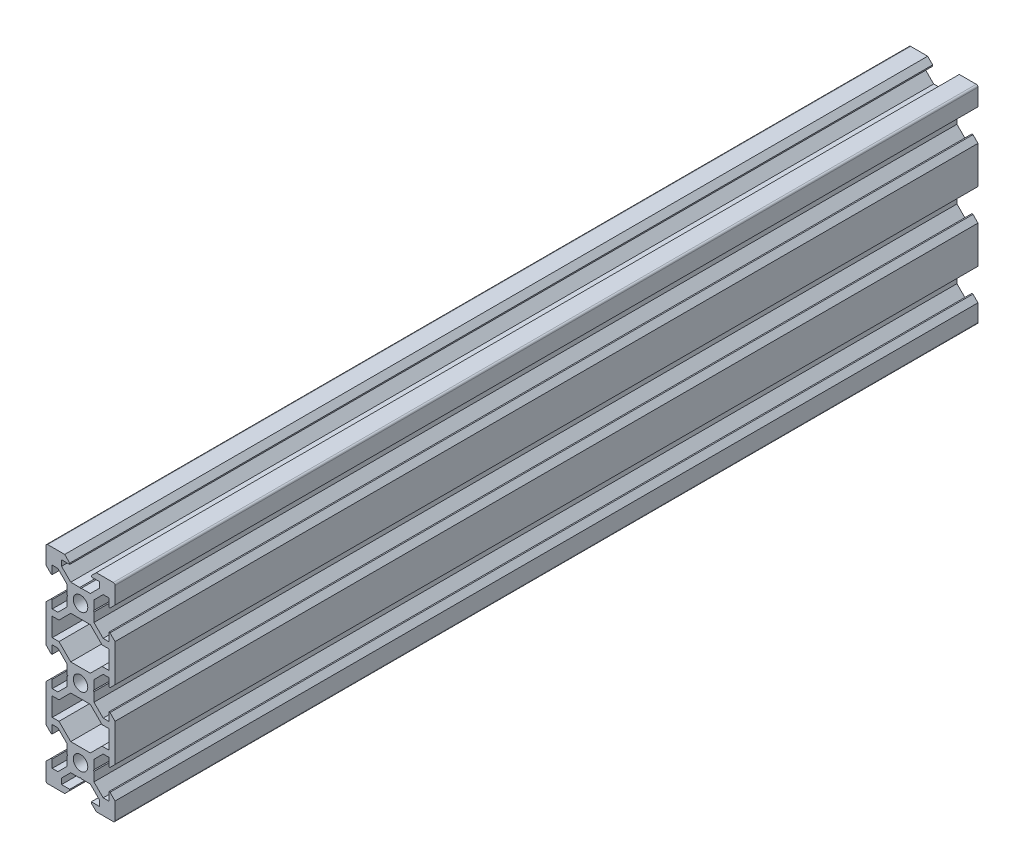
SolidWorks part; units mm, degrees
material "6061-T6 (SS)"
ref_plane "Front Plane" through (0, 0, 0) normal (0, 0, 1) x (1, 0, 0)
ref_plane "Top Plane" through (0, 0, 0) normal (0, 1, 0) x (1, 0, 0)
ref_plane "Right Plane" through (0, 0, 0) normal (1, 0, 0) x (0, 0, -1)
sketch "Sketch1" plane through (0, 0, 0) normal (0, 0, 1) x (1, 0, 0)
  line L0 (0, 0) -> (10, 0) construction
  line L1 (9.5, -30) -> (-9.5, -30)
  line L2 (10, -29.5) -> (10, 29.5)
  line L3 (9.5, 30) -> (-9.5, 30)
  line L4 (-10, -29.5) -> (-10, 29.5)
  line L5 (10, -30) -> (-10, 30) construction
  line L6 (10, 30) -> (-10, -30) construction
  circle A0 centre (0, 20) radius 2.1
  circle A1 centre (0, 0) radius 2.1
  circle A2 centre (0, -20) radius 2.1
  arc A3 (-9.5, -30) -> (-10, -29.5) centre (-9.5, -29.5) cw
  arc A4 (9.5, -30) -> (10, -29.5) centre (9.5, -29.5) ccw
  arc A5 (10, 29.5) -> (9.5, 30) centre (9.5, 29.5) ccw
  arc A6 (-9.5, 30) -> (-10, 29.5) centre (-9.5, 29.5) ccw
  point P0 (0, 0)
  line B0 (0, 20) -> (0, 30) construction
  line B1 (0, 23.69) -> (-0.21, 23.9)
  line B2 (-0.21, 23.9) -> (-2.8393, 23.9)
  line B3 (-2.8393, 23.9) -> (-5.5, 26.5607)
  line B4 (-5.5, 26.5607) -> (-5.5, 28.2)
  line B5 (-5.5, 28.2) -> (-3.125, 28.2)
  line B6 (-3.125, 28.2) -> (-3.125, 28.545)
  line B7 (-3.125, 28.545) -> (-4.58, 30)
  line B8 (-4.58, 30) -> (4.58, 30)
  line B9 (0, 20) -> (-5.9132, 25.9132) construction
  line B10 (3.125, 28.545) -> (4.58, 30)
  line B11 (3.125, 28.2) -> (3.125, 28.545)
  line B12 (5.5, 28.2) -> (3.125, 28.2)
  line B13 (5.5, 26.5607) -> (5.5, 28.2)
  line B14 (2.8393, 23.9) -> (5.5, 26.5607)
  line B15 (0.21, 23.9) -> (2.8393, 23.9)
  line B16 (0, 23.69) -> (0.21, 23.9)
  line B17 (0, 20) -> (-10, 20) construction
  line B18 (-3.69, 20) -> (-3.9, 19.79)
  line B19 (-3.9, 19.79) -> (-3.9, 17.1607)
  line B20 (-3.9, 17.1607) -> (-6.5607, 14.5)
  line B21 (-6.5607, 14.5) -> (-8.2, 14.5)
  line B22 (-8.2, 14.5) -> (-8.2, 16.875)
  line B23 (-8.2, 16.875) -> (-8.545, 16.875)
  line B24 (-8.545, 16.875) -> (-10, 15.42)
  line B25 (-10, 15.42) -> (-10, 24.58)
  line B26 (0, 20) -> (-5.9132, 14.0868) construction
  line B27 (-8.545, 23.125) -> (-10, 24.58)
  line B28 (-8.2, 23.125) -> (-8.545, 23.125)
  line B29 (-8.2, 25.5) -> (-8.2, 23.125)
  line B30 (-6.5607, 25.5) -> (-8.2, 25.5)
  line B31 (-3.9, 22.8393) -> (-6.5607, 25.5)
  line B32 (-3.9, 20.21) -> (-3.9, 22.8393)
  line B33 (-3.69, 20) -> (-3.9, 20.21)
  line B34 (0, 0) -> (-10, 0) construction
  line B35 (-3.69, 0) -> (-3.9, -0.21)
  line B36 (-3.9, -0.21) -> (-3.9, -2.8393)
  line B37 (-3.9, -2.8393) -> (-6.5607, -5.5)
  line B38 (-6.5607, -5.5) -> (-8.2, -5.5)
  line B39 (-8.2, -5.5) -> (-8.2, -3.125)
  line B40 (-8.2, -3.125) -> (-8.545, -3.125)
  line B41 (-8.545, -3.125) -> (-10, -4.58)
  line B42 (-10, -4.58) -> (-10, 4.58)
  line B43 (0, 0) -> (-5.9132, -5.9132) construction
  line B44 (-8.545, 3.125) -> (-10, 4.58)
  line B45 (-8.2, 3.125) -> (-8.545, 3.125)
  line B46 (-8.2, 5.5) -> (-8.2, 3.125)
  line B47 (-6.5607, 5.5) -> (-8.2, 5.5)
  line B48 (-3.9, 2.8393) -> (-6.5607, 5.5)
  line B49 (-3.9, 0.21) -> (-3.9, 2.8393)
  line B50 (-3.69, 0) -> (-3.9, 0.21)
  line B51 (0, -20) -> (-10, -20) construction
  line B52 (-3.69, -20) -> (-3.9, -20.21)
  line B53 (-3.9, -20.21) -> (-3.9, -22.8393)
  line B54 (-3.9, -22.8393) -> (-6.5607, -25.5)
  line B55 (-6.5607, -25.5) -> (-8.2, -25.5)
  line B56 (-8.2, -25.5) -> (-8.2, -23.125)
  line B57 (-8.2, -23.125) -> (-8.545, -23.125)
  line B58 (-8.545, -23.125) -> (-10, -24.58)
  line B59 (-10, -24.58) -> (-10, -15.42)
  line B60 (0, -20) -> (-5.9132, -25.9132) construction
  line B61 (-8.545, -16.875) -> (-10, -15.42)
  line B62 (-8.2, -16.875) -> (-8.545, -16.875)
  line B63 (-8.2, -14.5) -> (-8.2, -16.875)
  line B64 (-6.5607, -14.5) -> (-8.2, -14.5)
  line B65 (-3.9, -17.1607) -> (-6.5607, -14.5)
  line B66 (-3.9, -19.79) -> (-3.9, -17.1607)
  line B67 (-3.69, -20) -> (-3.9, -19.79)
  line B68 (0, -20) -> (0, -30) construction
  line B69 (0, -23.69) -> (0.21, -23.9)
  line B70 (0.21, -23.9) -> (2.8393, -23.9)
  line B71 (2.8393, -23.9) -> (5.5, -26.5607)
  line B72 (5.5, -26.5607) -> (5.5, -28.2)
  line B73 (5.5, -28.2) -> (3.125, -28.2)
  line B74 (3.125, -28.2) -> (3.125, -28.545)
  line B75 (3.125, -28.545) -> (4.58, -30)
  line B76 (4.58, -30) -> (-4.58, -30)
  line B77 (0, -20) -> (5.9132, -25.9132) construction
  line B78 (-3.125, -28.545) -> (-4.58, -30)
  line B79 (-3.125, -28.2) -> (-3.125, -28.545)
  line B80 (-5.5, -28.2) -> (-3.125, -28.2)
  line B81 (-5.5, -26.5607) -> (-5.5, -28.2)
  line B82 (-2.8393, -23.9) -> (-5.5, -26.5607)
  line B83 (-0.21, -23.9) -> (-2.8393, -23.9)
  line B84 (0, -23.69) -> (-0.21, -23.9)
  line B85 (0, -20) -> (10, -20) construction
  line B86 (3.69, -20) -> (3.9, -19.79)
  line B87 (3.9, -19.79) -> (3.9, -17.1607)
  line B88 (3.9, -17.1607) -> (6.5607, -14.5)
  line B89 (6.5607, -14.5) -> (8.2, -14.5)
  line B90 (8.2, -14.5) -> (8.2, -16.875)
  line B91 (8.2, -16.875) -> (8.545, -16.875)
  line B92 (8.545, -16.875) -> (10, -15.42)
  line B93 (10, -15.42) -> (10, -24.58)
  line B94 (0, -20) -> (5.9132, -14.0868) construction
  line B95 (8.545, -23.125) -> (10, -24.58)
  line B96 (8.2, -23.125) -> (8.545, -23.125)
  line B97 (8.2, -25.5) -> (8.2, -23.125)
  line B98 (6.5607, -25.5) -> (8.2, -25.5)
  line B99 (3.9, -22.8393) -> (6.5607, -25.5)
  line B100 (3.9, -20.21) -> (3.9, -22.8393)
  line B101 (3.69, -20) -> (3.9, -20.21)
  line B102 (0, 0) -> (10, 0) construction
  line B103 (3.69, 0) -> (3.9, 0.21)
  line B104 (3.9, 0.21) -> (3.9, 2.8393)
  line B105 (3.9, 2.8393) -> (6.5607, 5.5)
  line B106 (6.5607, 5.5) -> (8.2, 5.5)
  line B107 (8.2, 5.5) -> (8.2, 3.125)
  line B108 (8.2, 3.125) -> (8.545, 3.125)
  line B109 (8.545, 3.125) -> (10, 4.58)
  line B110 (10, 4.58) -> (10, -4.58)
  line B111 (0, 0) -> (5.9132, 5.9132) construction
  line B112 (8.545, -3.125) -> (10, -4.58)
  line B113 (8.2, -3.125) -> (8.545, -3.125)
  line B114 (8.2, -5.5) -> (8.2, -3.125)
  line B115 (6.5607, -5.5) -> (8.2, -5.5)
  line B116 (3.9, -2.8393) -> (6.5607, -5.5)
  line B117 (3.9, -0.21) -> (3.9, -2.8393)
  line B118 (3.69, 0) -> (3.9, -0.21)
  line B119 (0, 20) -> (10, 20) construction
  line B120 (3.69, 20) -> (3.9, 20.21)
  line B121 (3.9, 20.21) -> (3.9, 22.8393)
  line B122 (3.9, 22.8393) -> (6.5607, 25.5)
  line B123 (6.5607, 25.5) -> (8.2, 25.5)
  line B124 (8.2, 25.5) -> (8.2, 23.125)
  line B125 (8.2, 23.125) -> (8.545, 23.125)
  line B126 (8.545, 23.125) -> (10, 24.58)
  line B127 (10, 24.58) -> (10, 15.42)
  line B128 (0, 20) -> (5.9132, 25.9132) construction
  line B129 (8.545, 16.875) -> (10, 15.42)
  line B130 (8.2, 16.875) -> (8.545, 16.875)
  line B131 (8.2, 14.5) -> (8.2, 16.875)
  line B132 (6.5607, 14.5) -> (8.2, 14.5)
  line B133 (3.9, 17.1607) -> (6.5607, 14.5)
  line B134 (3.9, 19.79) -> (3.9, 17.1607)
  line B135 (3.69, 20) -> (3.9, 19.79)
  line B136 (-8.2, 7.3) -> (-8.2, 12.7)
  line B137 (-8.2, 12.7) -> (-6.2393, 12.7)
  line B138 (-6.2393, 12.7) -> (-2.8393, 16.1)
  line B139 (-2.8393, 16.1) -> (2.8393, 16.1)
  line B140 (0, 16.1) -> (0, 10) construction
  line B141 (0, 10) -> (-8.2, 10) construction
  line B142 (6.2393, 12.7) -> (2.8393, 16.1)
  line B143 (8.2, 12.7) -> (6.2393, 12.7)
  line B144 (8.2, 7.3) -> (8.2, 12.7)
  line B145 (8.2, 7.3) -> (6.2393, 7.3)
  line B146 (6.2393, 7.3) -> (2.8393, 3.9)
  line B147 (-2.8393, 3.9) -> (2.8393, 3.9)
  line B148 (-6.2393, 7.3) -> (-2.8393, 3.9)
  line B149 (-8.2, 7.3) -> (-6.2393, 7.3)
  line B150 (0, 16.1) -> (0, 20) construction
  line B151 (0, 20) -> (-5.0927, 14.9073) construction
  line B152 (-8.2, -12.7) -> (-8.2, -7.3)
  line B153 (-8.2, -7.3) -> (-6.2393, -7.3)
  line B154 (-6.2393, -7.3) -> (-2.8393, -3.9)
  line B155 (-2.8393, -3.9) -> (2.8393, -3.9)
  line B156 (0, -3.9) -> (0, -10) construction
  line B157 (0, -10) -> (-8.2, -10) construction
  line B158 (6.2393, -7.3) -> (2.8393, -3.9)
  line B159 (8.2, -7.3) -> (6.2393, -7.3)
  line B160 (8.2, -12.7) -> (8.2, -7.3)
  line B161 (8.2, -12.7) -> (6.2393, -12.7)
  line B162 (6.2393, -12.7) -> (2.8393, -16.1)
  line B163 (-2.8393, -16.1) -> (2.8393, -16.1)
  line B164 (-6.2393, -12.7) -> (-2.8393, -16.1)
  line B165 (-8.2, -12.7) -> (-6.2393, -12.7)
  line B166 (0, -3.9) -> (0, 0) construction
  line B167 (0, 0) -> (-5.0927, -5.0927) construction
  dimension "D3" = 4.2
  dimension "D5" = 0.5
  dimension "D1" = 20
  dimension "D2" = 60
  dimension "D4" = 40
sketch_block_instance "V Slot 1-4"
sketch_block "V Slot 1" parameters "D1"=10, "D2"=11, "D3"=4.3, "D4"=1.8, "D5"=0.21, "D6"=45, "D7"=9.16, "D8"=1.5, "D9"=6.25
sketch_block_instance "V Slot 1-5"
sketch_block_instance "V Slot 1-6"
sketch_block_instance "V Slot 1-7"
sketch_block_instance "V Slot 1-8"
sketch_block_instance "V Slot 1-9"
sketch_block_instance "V Slot 1-10"
sketch_block_instance "V Slot 1-11"
sketch_block_instance "Center Cutout 1-1"
sketch_block "Center Cutout 1" parameters "D1"=5.4, "D2"=12.2, "D3"=8.2, "D4"=45, "D5"=10, "D6"=1.5
sketch_block_instance "Center Cutout 1-2"
extrude "Boss-Extrude1" add sketch "Sketch1" along normal blind 250 contours B135 B120 B121 B122 B123 B124 B125 B126 L2 A5 L3 B10 B11 B12 B13 B14 B15 B16 B1 B2 B3 B4 B5 B6 B7 A6 L4 B27 B28 B29 B30 B31 B32 B33 B18 B19 B20 B21 B22 B23 B24 B44 B45 B46 B47 B48 B49 B50 B35
